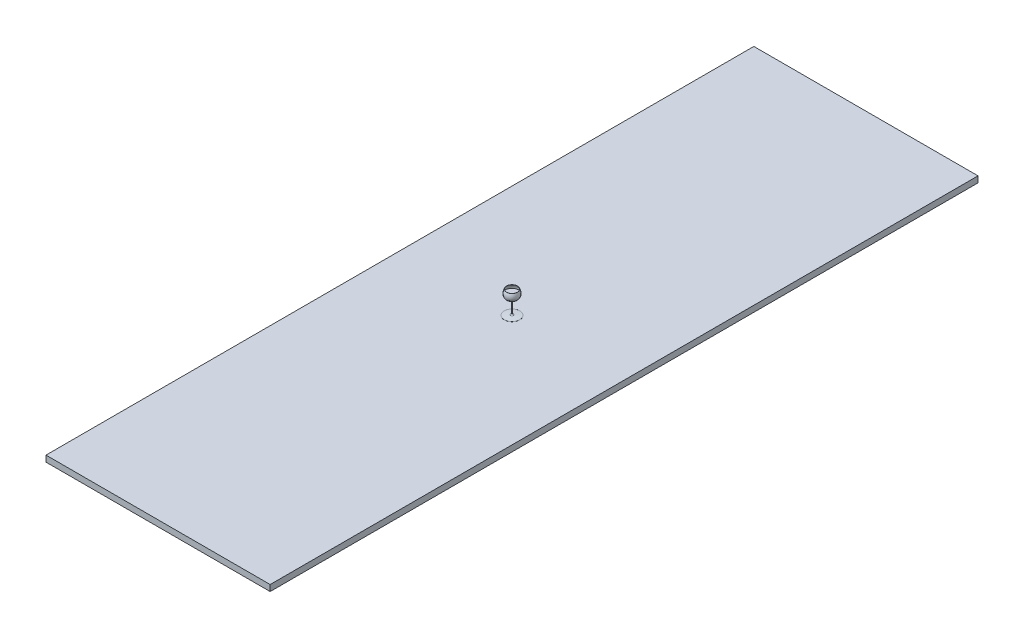
SolidWorks part; units mm, degrees
other "Kamera1"
ref_plane "Ebene vorne" through (0, 0, 0) normal (0, 0, 1) x (1, 0, 0)
ref_plane "Ebene oben" through (0, 0, 0) normal (0, 1, 0) x (1, 0, 0)
ref_plane "Ebene rechts" through (0, 0, 0) normal (1, 0, 0) x (0, 0, -1)
sketch "Skizze1" plane through (0, 0, 0) normal (0, 0, 1) x (1, 0, 0)
  line L0 (0, 82.3672) -> (0, -83.0844) construction
  line L1 (0, -0.3586) -> (0, 0.654)
  arc A0 (44.6113, 77.1231) -> (43.732, 76.6468) centre (44.1716, 76.8849) ccw
  spline S0 degree 3 poles (44.6113, 77.1231) (62.9846, 43.2054) (52.5835, 8.0095) (0, -0.3586) knots 0 0 0 0 1 1 1 1
  spline S1 degree 1 poles (43.732, 76.6468) (-0.1572, 0.6289) knots 0 0 1 1 construction
  spline S2 degree 3 poles (43.732, 76.6468) (44.2935, 75.6102) (45.3813, 73.4971) (47.3083, 69.3112) (49.2935, 64.0785) (50.9655, 57.8693) (52.2308, 49.7292) (51.9624, 39.9224) (48.5558, 29.0463) (43.0172, 20.9507) (36.865, 15.1972) (31.3634, 11.2845) (24.9494, 7.8167) (18.8249, 5.3345) (13.4463, 3.6154) (9.1718, 2.4652) (5.402, 1.6264) (2.2718, 1.0317) (0.649, 0.7572) (-0.1572, 0.6289) knots 0 0 0 0 0.03125 0.0625 0.125 0.1875 0.25 0.375 0.5 0.625 0.6875 0.75 0.8125 0.875 0.90625 0.9375 0.96875 0.984375 1 1 1 1 only from (43.732, 76.6468) to (0, 0.654)
  dimension "D1" = 1
revolve "Rotation1" add sketch "Skizze1" angle 360 about L0
sketch "Skizze2" plane through (0, 0, 0) normal (0, 0, 1) x (1, 0, 0)
  line L0 (0, 118.7793) -> (0, -107.9161) construction
  line L1 (3.1492, 0.1837) -> (3.1492, -102.9991)
  line L2 (3.1492, -102.9991) -> (63.0142, -107.9161)
  line L4 (63.0142, -109.1161) -> (0, -109.1161)
  line L5 (0, -109.1161) -> (0, -0.3586)
  arc A0 (63.0142, -107.9161) -> (63.0142, -109.1161) centre (63.0142, -108.5161) cw
  spline S0 degree 3 poles (-2374.6125, 1797.4269) (1969.1045, -2523.4486) (-871.1718, 3091.7392) (-724.9586, -2676.5985) knots -3.295874 -3.295874 -3.295874 -3.295874 5.824109 5.824109 5.824109 5.824109 only from (0, -0.3586) to (44.6113, 77.1231) construction
  spline S1 degree 3 poles (0, -0.3586) (1.0671, -0.1888) (2.1167, -0.008) (3.1492, 0.1837) knots 0 0 0 0 0.020293 0.020293 0.020293 0.020293
  dimension "D1" = 1.2
revolve "Rotation2" add sketch "Skizze2" angle 360 about L0
fillet "Verrundung1" radius 10 1 edges at (0, -102.9991, 3.1492)
fillet "Verrundung2" radius 10 1 edges at (0, 0.1837, 3.1492)
sketch "Skizze7" plane through (0, 0, 0) normal (0, 0, 1) x (1, 0, 0)
  line L0 (-65.759, 46.3619) -> (66.2461, 46.3619)
  line L1 (-92.3058, 46.3619) -> (127.0658, 46.3619) construction
split line "Trennlinie7"
ref_plane "Ebene3" through (0, 46.3619, 0) normal (0, 1, 0) x (1, 0, 0)
sketch "Skizze17" plane through (0, 46.3619, 0) normal (0, 1, 0) x (1, 0, 0)
  circle A0 centre (0, 0) radius 52.0096 construction
  circle A1 centre (0, 0) radius 52.0096
extrude "Aufsatz-Linear austragen7" add sketch "Skizze17" against normal up to next
sketch "Skizze12" plane through (0, -109.1161, 0) normal (0, -1, 0) x (1, 0, 0)
  line L1 (-914.925, -2889.1814) -> (914.925, -2889.1814)
  line L2 (-914.925, -2889.1814) -> (-914.925, 2889.1814)
  line L3 (-914.925, 2889.1814) -> (914.925, 2889.1814)
  line L4 (914.925, -2889.1814) -> (914.925, 2889.1814)
  line L5 (-914.925, -2889.1814) -> (914.925, 2889.1814) construction
  line L6 (-914.925, 2889.1814) -> (914.925, -2889.1814) construction
  point P0 (0, 0)
extrude "Aufsatz-Linear austragen2" add sketch "Skizze12" along normal blind 50
